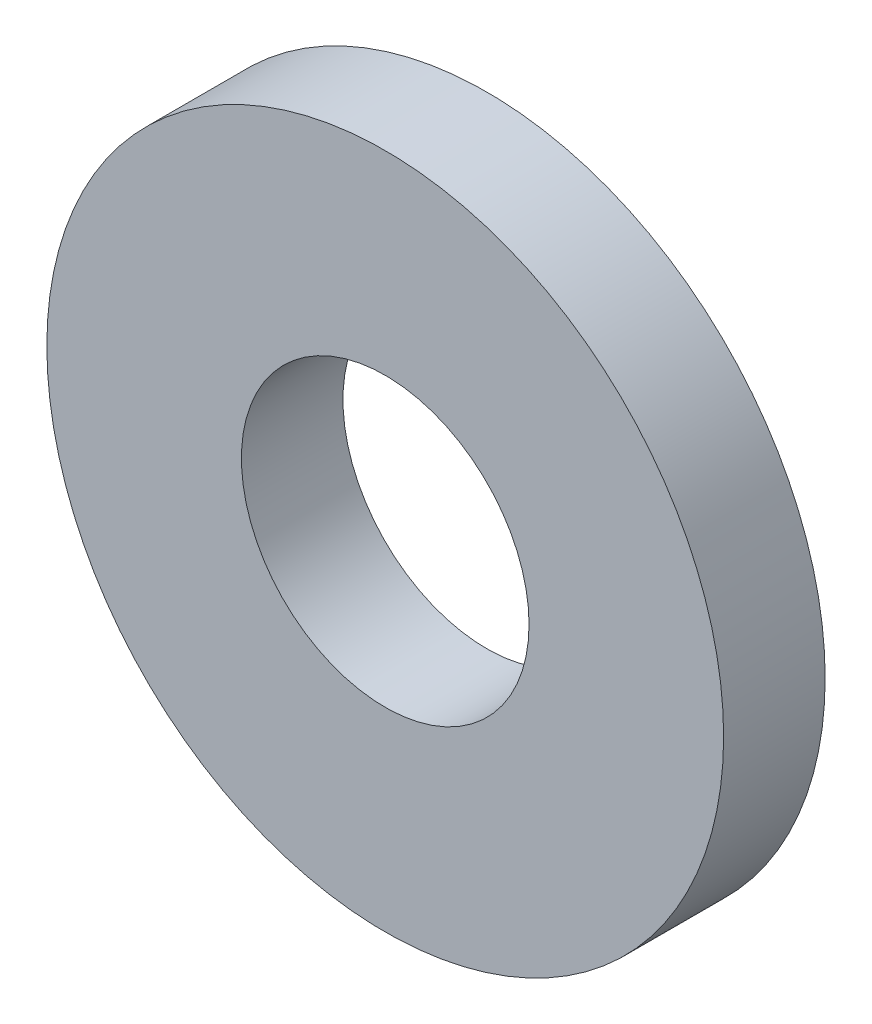
SolidWorks part; units mm, degrees
material "Plain Carbon Steel"
ref_plane "Front Plane" through (0, 0, 0) normal (0, 0, 1) x (1, 0, 0)
ref_plane "Top Plane" through (0, 0, 0) normal (0, 1, 0) x (1, 0, 0)
ref_plane "Right Plane" through (0, 0, 0) normal (1, 0, 0) x (0, 0, -1)
sketch "Sketch1" plane through (0, 0, 0) normal (0, 0, 1) x (1, 0, 0)
  line L0 (350, 40) -> (350, 120) construction
  line L2 (-660, 120) -> (660, 120) construction
  line L4 (350, -26.675) -> (350, 26.675) construction
  line L6 (350, 107) -> (350, 58.5) construction
  line L7 (310, 40) -> (385, 40) construction
  circle A0 centre (350, 80) radius 20
  circle A1 centre (350, 80) radius 8.5
  dimension "D1" = 40
  dimension "D2" = 17
extrude "Boss-Extrude1" add sketch "Sketch1" along normal blind 6
ref_point "Point1"
ref_plane "Plane1" through (350, 0, 0) normal (1, 0, 0) x (0, 0, -1)
ref_plane "Plane2" through (175, 0, 0) normal (1, 0, 0) x (0, 0, -1)
